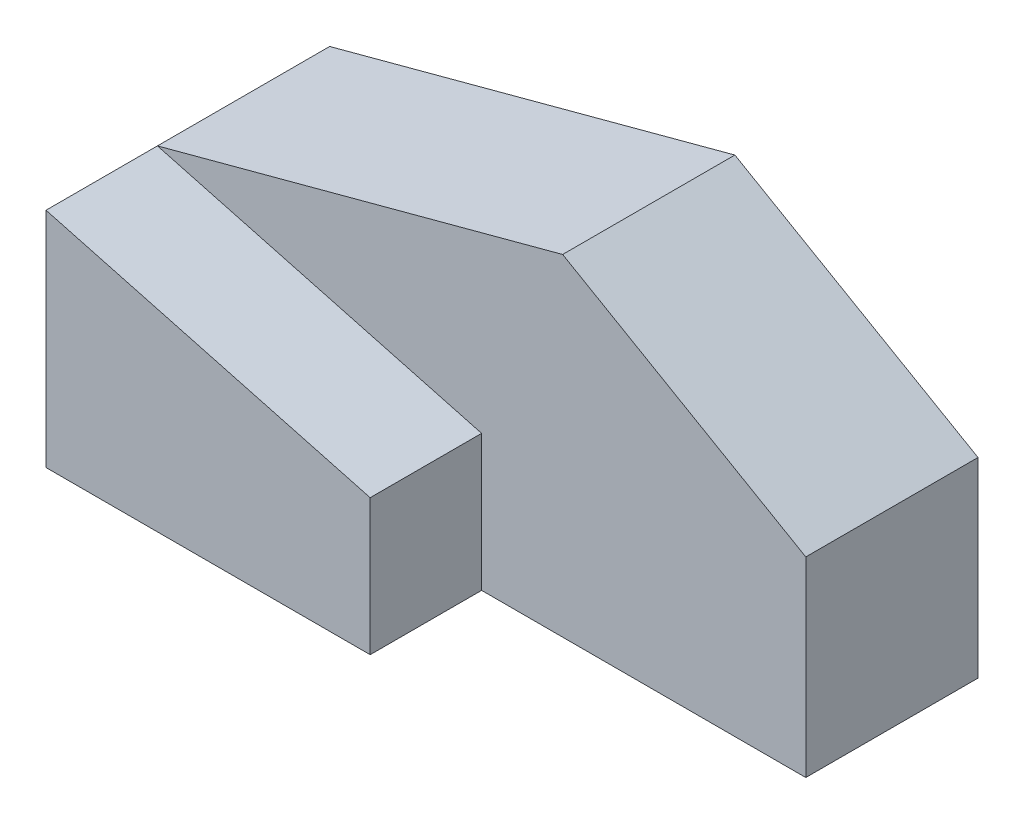
SolidWorks part; units mm, degrees
ref_plane "Front Plane" through (0, 0, 0) normal (0, 0, 1) x (1, 0, 0)
ref_plane "Top Plane" through (0, 0, 0) normal (0, 1, 0) x (1, 0, 0)
ref_plane "Right Plane" through (0, 0, 0) normal (1, 0, 0) x (0, 0, -1)
sketch "Sketch1" plane through (0, 0, 0) normal (0, 0, 1) x (1, 0, 0)
  line L0 (50.8, 0) -> (-50.8, 0)
  line L1 (-50.8, 0) -> (-50.8, 34.925)
  line L2 (-50.8, 34.925) -> (12.7, 51.9398)
  line L3 (12.7, 51.9398) -> (50.8, 29.9427)
  line L4 (50.8, 29.9427) -> (50.8, 0)
  line L5 (-50.8, 34.925) -> (0, 21.3132) construction
  line L6 (0, 21.3132) -> (0, 0) construction
  dimension "D1" = 101.6
  dimension "D2" = 63.5
  dimension "D3" = 34.925
  dimension "D4" = 135
  dimension "D5" = 50.8
  dimension "D6" = 105
  dimension "D7" = 30
extrude "Boss-Extrude1" add sketch "Sketch1" along normal mid plane 26.9875
sketch "Sketch2" plane through (0, 0, 13.4937) normal (0, 0, 1) x (1, 0, 0)
  line L0 (-50.8, 0) -> (-50.8, 34.925)
  line L1 (0, 21.3132) -> (0, 0)
  line L2 (-50.8, 0) -> (50.8, 0) construction
  line L3 (0, 0) -> (-50.8, 0)
  line L4 (-50.8, 34.925) -> (-50.8, 0) construction
  line L6 (12.7, 51.9398) -> (-50.8, 34.925) construction
  line L7 (-50.8, 34.925) -> (0, 21.3132)
  dimension "D1" = 34.925
  dimension "D2" = 50.8
  dimension "D3" = 30
extrude "Boss-Extrude2" add sketch "Sketch2" along normal blind 17.4625
